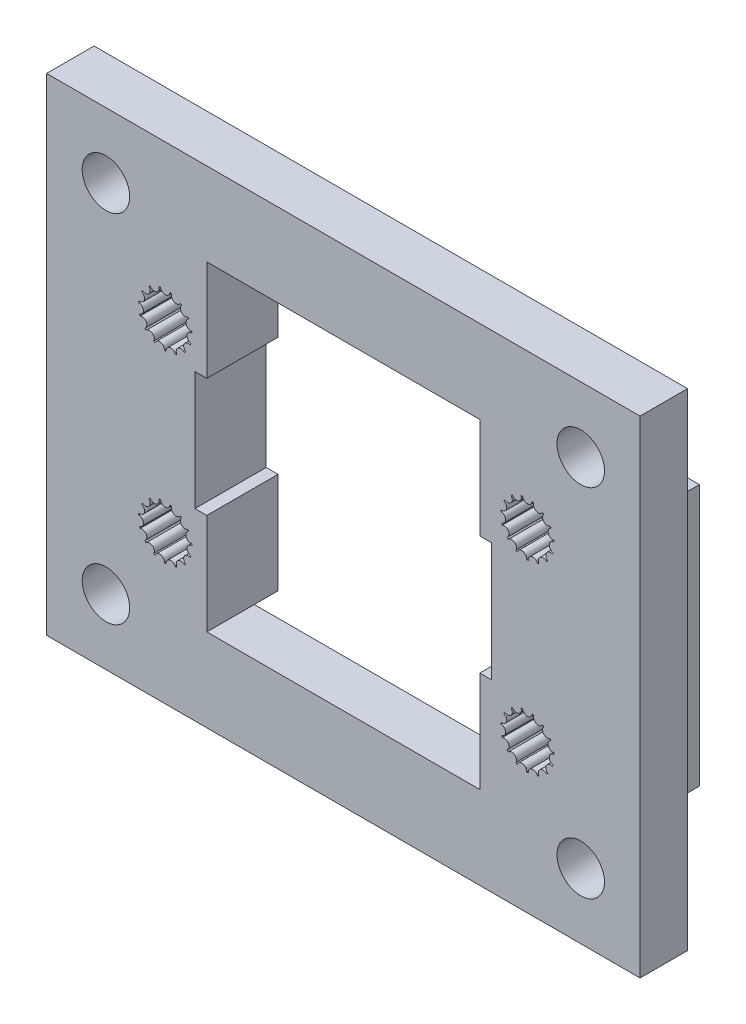
SolidWorks part; units mm, degrees
ref_plane "Front Plane" through (0, 0, 0) normal (0, 0, 1) x (1, 0, 0)
ref_plane "Top Plane" through (0, 0, 0) normal (0, 1, 0) x (1, 0, 0)
ref_plane "Right Plane" through (0, 0, 0) normal (1, 0, 0) x (0, 0, -1)
sketch "Sketch3" plane through (0, 0, 0) normal (0, 0, 1) x (1, 0, 0)
  line L0 (-10, 25) -> (40, 25)
  line L1 (0, 0) -> (30, 0)
  line L2 (0, 0) -> (0, 15)
  line L3 (0, 15) -> (30, 15)
  line L4 (30, 0) -> (30, 15)
  line L5 (40, -10) -> (40, 25)
  line L6 (-10, -10) -> (40, -10)
  line L7 (-10, -10) -> (-10, 25)
  dimension "D1" = 10
extrude "Boss-Extrude2" add sketch "Sketch3" along normal blind 10 contours L7 L0 L5 L6
sketch "Sketch1" plane through (0, 0, 0) normal (0, 0, 1) x (1, 0, 0)
  line L1 (0, 0) -> (30, 0) construction
  line L2 (0, 0) -> (0, 15) construction
  line L3 (0, 15) -> (30, 15) construction
  line L4 (30, 0) -> (30, 15) construction
  arc A0 (-0.3984, 17.2144) -> (0.3984, 17.2144) centre (0, 15) ccw
  arc A1 (-0.3984, 17.2144) -> (0.3984, 17.2144) centre (0, 17.25) ccw
  arc A2 (0.5367, 17.185) -> (1.2647, 16.8609) centre (0.9152, 17.0555) ccw
  arc A3 (0.5367, 17.185) -> (1.2647, 16.8609) centre (0, 15) ccw
  arc A4 (1.3791, 16.7778) -> (1.9122, 16.1857) centre (1.6721, 16.5055) ccw
  arc A5 (1.3791, 16.7778) -> (1.9122, 16.1857) centre (0, 15) ccw
  arc A6 (1.9829, 16.0632) -> (2.2292, 15.3054) centre (2.1399, 15.6953) ccw
  arc A7 (1.9829, 16.0632) -> (2.2292, 15.3054) centre (0, 15) ccw
  arc A8 (2.244, 15.1648) -> (2.1607, 14.3723) centre (2.2377, 14.7648) ccw
  arc A9 (2.244, 15.1648) -> (2.1607, 14.3723) centre (0, 15) ccw
  arc A10 (2.117, 14.2378) -> (1.7186, 13.5477) centre (1.9486, 13.875) ccw
  arc A11 (2.117, 14.2378) -> (1.7186, 13.5477) centre (0, 15) ccw
  arc A12 (1.6239, 13.4427) -> (0.9793, 12.9743) centre (1.3225, 13.1797) ccw
  arc A13 (1.6239, 13.4427) -> (0.9793, 12.9743) centre (0, 15) ccw
  arc A14 (0.8501, 12.9168) -> (0.0707, 12.7511) centre (0.4678, 12.7992) ccw
  arc A15 (0.8501, 12.9168) -> (0.0707, 12.7511) centre (0, 15) ccw
  arc A16 (-0.0707, 12.7511) -> (-0.8501, 12.9168) centre (-0.4678, 12.7992) ccw
  arc A17 (-0.0707, 12.7511) -> (-0.8501, 12.9168) centre (0, 15) ccw
  arc A18 (-0.9793, 12.9743) -> (-1.6239, 13.4427) centre (-1.3225, 13.1797) ccw
  arc A19 (-0.9793, 12.9743) -> (-1.6239, 13.4427) centre (0, 15) ccw
  arc A20 (-1.7186, 13.5477) -> (-2.117, 14.2378) centre (-1.9486, 13.875) ccw
  arc A21 (-1.7186, 13.5477) -> (-2.117, 14.2378) centre (0, 15) ccw
  arc A22 (-2.1607, 14.3723) -> (-2.244, 15.1648) centre (-2.2377, 14.7648) ccw
  arc A23 (-2.1607, 14.3723) -> (-2.244, 15.1648) centre (0, 15) ccw
  arc A24 (-2.2292, 15.3054) -> (-1.9829, 16.0632) centre (-2.1399, 15.6953) ccw
  arc A25 (-2.2292, 15.3054) -> (-1.9829, 16.0632) centre (0, 15) ccw
  arc A26 (-1.9122, 16.1857) -> (-1.3791, 16.7778) centre (-1.6721, 16.5055) ccw
  arc A27 (-1.9122, 16.1857) -> (-1.3791, 16.7778) centre (0, 15) ccw
  arc A28 (-1.2647, 16.8609) -> (-0.5367, 17.185) centre (-0.9152, 17.0555) ccw
  arc A29 (-1.2647, 16.8609) -> (-0.5367, 17.185) centre (0, 15) ccw
  point P52 (0, 15)
  dimension "D3" = 4.5
  dimension "D4" = 0.8
  dimension "D1" = 30
  dimension "D2" = 15
  dimension "D5" = 15
extrude "Cut-Extrude1" cut sketch "Sketch1" along normal blind 16 contours A28 A0 A26 A24 A22 A20 A18 A16 A14 A12 A10 A8 A6 A4 A2 A1
pattern_linear "LPattern1" count 2 spacing 15.5 along (0, -1, 0) count 2 spacing 30.51 along (1, 0, 0) of "Cut-Extrude1"
sketch "Sketch4" plane through (0, 0, 0) normal (0, 0, -1) x (-1, 0, 0)
  line L0 (-36, 21) -> (6, 21)
  line L1 (-40, -10) -> (10, -10)
  line L2 (-40, -10) -> (-40, 25)
  line L3 (-40, 25) -> (10, 25)
  line L4 (10, -10) -> (10, 25)
  line L5 (6, -6) -> (6, 21)
  line L6 (-36, -6) -> (6, -6)
  line L7 (-36, -6) -> (-36, 21)
  dimension "D1" = 4
extrude "Cut-Extrude2" cut sketch "Sketch4" against normal blind 6
sketch "Sketch5" plane through (0, 0, 0) normal (0, 0, -1) x (-1, 0, 0)
  line L0 (-27.5, 2.5) -> (-27.5, 12.5)
  line L1 (-36, -6) -> (6, -6)
  line L2 (-36, -6) -> (-36, 21)
  line L3 (-36, 21) -> (6, 21)
  line L4 (6, -6) -> (6, 21)
  line L5 (-27.5, 12.5) -> (-2.5, 12.5)
  line L6 (-2.5, 2.5) -> (-2.5, 12.5)
  line L7 (-27.5, 2.5) -> (-2.5, 2.5)
  dimension "D1" = 8.5
extrude "Cut-Extrude4" cut sketch "Sketch5" against normal blind 24 contours L5 L6 L7 L0
sketch "Sketch6" plane through (0, 0, 6) normal (0, 0, -1) x (-1, 0, 0)
  line L0 (-15, 12.5) -> (-2.5, 7.5) construction
  line L1 (-27.5, 12.5) -> (-2.5, 12.5) construction
  line L2 (-2.5, 2.5) -> (-2.5, 12.5) construction
  line L3 (-2.5, 7.5) -> (-15, 7.5) construction
  line L4 (-15, 7.5) -> (-15, 25.6664) construction
  line L5 (-15, 7.5) -> (-40, 7.5) construction
  line L6 (-40, 25) -> (-40, -10) construction
  line L7 (-40, 7.5) -> (10, 7.5) construction
  line L8 (10, -10) -> (10, 25) construction
  circle A0 centre (5, 22.5) radius 2
  dimension "D1" = 4
  dimension "D2" = 20
  dimension "D3" = 15
extrude "Cut-Extrude5" cut sketch "Sketch6" along normal blind 24 and the other way blind 24 contours A0
sketch "Sketch7" plane through (0, 0, 6) normal (0, 0, -1) x (-1, 0, 0)
  line L1 (10, 25) -> (-40, 25) construction
  line L2 (5, 25) -> (10, 25)
  line L3 (10, 25) -> (10, 20.5)
  line L4 (10, -10) -> (10, 25) construction
  line L6 (1.2919, 21) -> (1.2919, 25)
  line L7 (3.6771, 21) -> (-36, 21) construction
  line L8 (1.2919, 25) -> (5, 25)
  line L9 (5, 18.5) -> (10, 18.5)
  line L10 (10, 18.5) -> (10, 20.5)
  arc A0 (1.2919, 21) -> (5, 18.5) centre (5, 22.5) ccw
  dimension "D1" = 8
extrude "Cut-Extrude6" cut sketch "Sketch7" along normal blind 24
ref_plane "Plane1" through (15, 0, 0) normal (-1, 0, 0) x (0, 0, 1)
ref_plane "Plane2" through (0, 7.5, 0) normal (0, -1, 0) x (-1, 0, 0)
mirror "Mirror1" about plane through (15, 0, 0) normal (-1, 0, 0) of "Cut-Extrude5", "Cut-Extrude6"
mirror "Mirror2" about plane through (0, 7.5, 0) normal (0, -1, 0) of "Cut-Extrude5", "Cut-Extrude6", "Mirror1"
sketch "Sketch9" plane through (0, 0, 6) normal (0, 0, -1) x (-1, 0, 0)
  line L0 (10, -10) -> (10, 25) construction
  line L1 (-40, -13) -> (10, -13)
  line L2 (-40, -13) -> (-40, 28)
  line L3 (-40, 28) -> (10, 28)
  line L4 (10, -13) -> (10, 28)
  line L5 (10, 25) -> (-40, 25) construction
  line L6 (-40, -10) -> (10, -10) construction
  line L7 (-40, 25) -> (-40, -10) construction
  line L8 (-2.5, 2.5) -> (-2.5, 12.5) construction
  line L9 (-27.5, 12.5) -> (-2.5, 12.5) construction
  line L10 (-27.5, 2.5) -> (-27.5, 12.5) construction
  line L11 (-27.5, 2.5) -> (-2.5, 2.5) construction
  line L12 (-2.5, 2.5) -> (-2.5, 12.5)
  line L13 (-27.5, 12.5) -> (-2.5, 12.5)
  line L14 (-27.5, 2.5) -> (-27.5, 12.5)
  line L15 (-27.5, 2.5) -> (-2.5, 2.5)
  circle A0 centre (5, -7.5) radius 2 construction
  circle A1 centre (-35, -7.5) radius 2 construction
  circle A2 centre (5, 22.5) radius 2 construction
  circle A3 centre (-35, 22.5) radius 2 construction
  circle A4 centre (5, -7.5) radius 2
  circle A5 centre (-35, -7.5) radius 2
  circle A6 centre (5, 22.5) radius 2
  circle A7 centre (-35, 22.5) radius 2
  line M7 (-40, -10) -> (10, -10)
  line M9 (10, 25) -> (-40, 25)
  dimension "D1" = 3
  dimension "D2" = 3
extrude "Boss-Extrude4" add sketch "Sketch9" against normal up to surface (4 mm away) contours L1 L4 L2 M7 | L4 L3 L2 M9 up to face at (37, -7.5, 10)
sketch "Sketch10" plane through (0, 0, 0) normal (0, 0, -1) x (-1, 0, 0)
  line L0 (-13.0739, 7.5) -> (-18.0697, 7.5) construction
  line L1 (-2.2, 7.5) -> (2.2, 7.5) construction
  line L2 (-18.0697, 7.5) -> (-15, 7.5) construction
  line L3 (-15, -5.5) -> (-15, 5.5) construction
  line L4 (-15, 7.5) -> (-15, 9.3565) construction
  line L6 (-36.5, -6.5) -> (6.5, -6.5)
  line L7 (-36.5, -6.5) -> (-36.5, 21.5)
  line L8 (-36.5, 21.5) -> (6.5, 21.5)
  line L9 (6.5, -6.5) -> (6.5, 21.5)
  line L10 (-36.5, -6.5) -> (6.5, 21.5) construction
  line L11 (-36.5, 21.5) -> (6.5, -6.5) construction
  dimension "D1" = 43
  dimension "D2" = 28
extrude "Cut-Extrude7" cut sketch "Sketch10" against normal blind 4 contours L7 L8 L9 L6
sketch "Sketch11" plane through (0, 0, 6) normal (0, 0, -1) x (-1, 0, 0)
  line L1 (6, -3.5) -> (8, -3.5)
  line L2 (6, -3.5) -> (6, 18.5)
  line L3 (6, 18.5) -> (8, 18.5)
  line L4 (8, -3.5) -> (8, 18.5)
  line L5 (-36, -3.5) -> (-38, -3.5)
  line L6 (-36, -3.5) -> (-36, 18.5)
  line L7 (-36, 18.5) -> (-38, 18.5)
  line L8 (-38, -3.5) -> (-38, 18.5)
  dimension "D1" = 2
  dimension "D2" = 2
extrude "Boss-Extrude5" add sketch "Sketch11" along normal blind 3
sketch "Sketch12" plane through (0, 0, 4) normal (0, 0, -1) x (-1, 0, 0)
  line L0 (-2.2, 7.5) -> (2.2, 7.5) construction
  line L1 (-3.5, -6) -> (-26.5, -6)
  line L2 (-3.5, -6) -> (-3.5, 21)
  line L3 (-3.5, 21) -> (-26.5, 21)
  line L4 (-26.5, -6) -> (-26.5, 21)
  line L5 (-3.5, -6) -> (-26.5, 21) construction
  line L6 (-3.5, 21) -> (-26.5, -6) construction
  line L7 (-15, -5.5) -> (-15, 5.5) construction
  line L8 (1.2919, -6) -> (-31.2919, -6) construction
  point P0 (-15, 7.5)
  dimension "D2" = 23
extrude "Cut-Extrude8" cut sketch "Sketch12" against normal blind 17
sketch "Sketch13" plane through (0, 0, 3) normal (0, 0, -1) x (-1, 0, 0)
  line L0 (-2.2, 7.5) -> (2.2, 7.5) construction
  line L1 (6.6, -8.7) -> (-36.6, -8.7)
  line L2 (6.6, -8.7) -> (6.6, 23.7)
  line L3 (6.6, 23.7) -> (-36.6, 23.7)
  line L4 (-36.6, -8.7) -> (-36.6, 23.7)
  line L5 (6.6, -8.7) -> (-36.6, 23.7) construction
  line L6 (6.6, 23.7) -> (-36.6, -8.7) construction
  line L7 (-15, -5.5) -> (-15, 5.5) construction
  line L8 (-36, -3.5) -> (-36, 18.5) construction
  circle A0 centre (-35, 22.5) radius 2 construction
  point P0 (-15, 7.5)
  dimension "D1" = 0.6
extrude "Cut-Extrude9" cut sketch "Sketch13" against normal up to surface (1 mm away) up to face at (30.4016, 7.5, 4)
